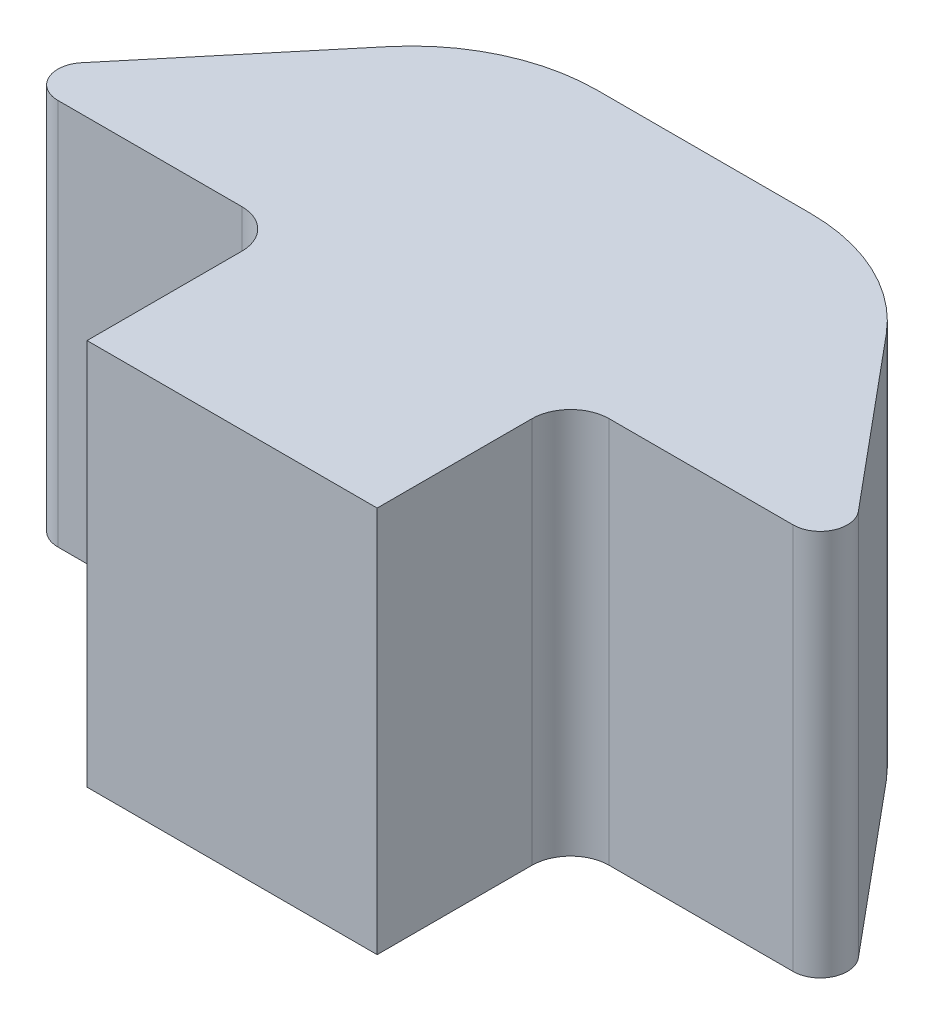
SolidWorks part; units mm, degrees
ref_plane "Front Plane" through (0, 0, 0) normal (0, 0, 1) x (1, 0, 0)
ref_plane "Top Plane" through (0, 0, 0) normal (0, 1, 0) x (1, 0, 0)
ref_plane "Right Plane" through (0, 0, 0) normal (1, 0, 0) x (0, 0, -1)
sketch "Sketch1" plane through (0, 0, 0) normal (0, 1, 0) x (1, 0, 0)
  line L0 (0, 0) -> (-5, 0)
  line L1 (-5, 0) -> (-11, -7.2)
  line L2 (-11, -7.2) -> (-3.75, -7.2)
  line L3 (-3.75, -7.2) -> (-3.75, -12.2)
  line L4 (-3.75, -12.2) -> (0, -12.2)
  line L5 (0, -12.2) -> (0, 0)
  dimension "D1" = 3.75
  dimension "D2" = 7.2
  dimension "D3" = 5
  dimension "D4" = 5
  dimension "D5" = 11
extrude "Boss-Extrude1" add sketch "Sketch1" along normal blind 10
fillet "Fillet1" radius 0.7 1 edges at (-11, 5, 7.2)
fillet "Fillet2" radius 1 1 edges at (-3.75, 5, 7.2)
mirror "Mirror1" about plane through (0, 10, 12.2) normal (-1, 0, 0) of "Fillet1", "Boss-Extrude1", "Fillet2"
fillet "Fillet3" radius 4.8 2 edges at (5, 5, 0) (-5, 5, 0)
